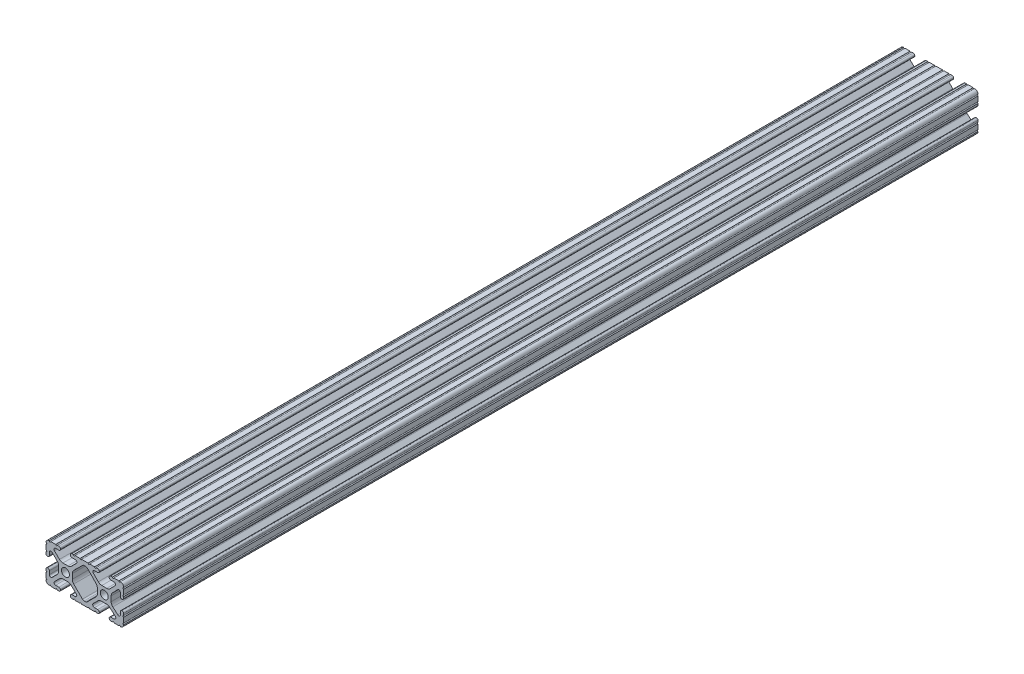
SolidWorks part; units mm, degrees
ref_plane "Front Plane" through (0, 0, 0) normal (0, 0, 1) x (1, 0, 0)
ref_plane "Top Plane" through (0, 0, 0) normal (0, 1, 0) x (1, 0, 0)
ref_plane "Right Plane" through (0, 0, 0) normal (1, 0, 0) x (0, 0, -1)
sketch "Sketch1" plane through (0, 0, 0) normal (0, 0, 1) x (1, 0, 0)
  line L0 (-7.2595, -3.8694) -> (-1.5457, -9.5728)
  line L1 (-8.1915, 1.6223) -> (-8.1915, -1.6223)
  line L2 (-1.504, 9.5765) -> (-7.252, 3.8768)
  line L3 (0.5515, 10.033) -> (-0.3952, 10.033)
  line L4 (7.2829, 3.8459) -> (1.6756, 9.5611)
  line L5 (8.1915, -1.6223) -> (8.1915, 1.6223)
  line L6 (1.5457, -9.5728) -> (7.2595, -3.8694)
  line L7 (-0.4332, -10.033) -> (0.4332, -10.033)
  line L8 (18.0171, 12.7) -> (16.9875, 12.7)
  line L9 (15.9385, 11.651) -> (15.9385, 11.5392)
  line L10 (16.9875, 10.4902) -> (19.1164, 10.4902)
  line L11 (19.8441, 8.7652) -> (16.619, 5.4551)
  line L12 (14.3449, 4.4958) -> (11.0833, 4.4958)
  line L13 (8.817, 5.4472) -> (5.5642, 8.7627)
  line L14 (6.2894, 10.4902) -> (8.4125, 10.4902)
  line L15 (9.4615, 11.5392) -> (9.4615, 11.651)
  line L16 (8.4125, 12.7) -> (7.3829, 12.7)
  line L17 (6.3669, 12.7) -> (3.1496, 12.7)
  line L18 (2.1336, 12.7) -> (-2.1336, 12.7)
  line L19 (-3.1496, 12.7) -> (-6.3669, 12.7)
  line L20 (-7.3829, 12.7) -> (-8.4125, 12.7)
  line L21 (-9.4615, 11.651) -> (-9.4615, 11.5392)
  line L22 (-8.4125, 10.4902) -> (-6.2836, 10.4902)
  line L23 (-5.5326, 8.6661) -> (-8.81, 5.4163)
  line L24 (-11.0455, 4.4958) -> (-14.3545, 4.4958)
  line L25 (-16.59, 5.4163) -> (-19.8674, 8.6661)
  line L26 (-19.1164, 10.4902) -> (-16.9875, 10.4902)
  line L27 (-15.9385, 11.5392) -> (-15.9385, 11.651)
  line L28 (-16.9875, 12.7) -> (-18.0171, 12.7)
  line L29 (-19.0331, 12.7) -> (-22.2504, 12.7)
  line L30 (-25.4, 9.5504) -> (-25.4, 6.3331)
  line L31 (-25.4, 5.3171) -> (-25.4, 4.2375)
  line L32 (-24.401, 3.2385) -> (-24.2392, 3.2385)
  line L33 (-23.1902, 4.2875) -> (-23.1902, 6.3347)
  line L34 (-21.434, 7.0665) -> (-18.148, 3.8082)
  line L35 (-17.2085, 1.5536) -> (-17.2085, -1.6952)
  line L36 (-18.1405, -3.9423) -> (-21.4316, -7.2274)
  line L37 (-23.1902, -6.498) -> (-23.1902, -4.2875)
  line L38 (-24.2392, -3.2385) -> (-24.351, -3.2385)
  line L39 (-25.4, -4.2875) -> (-25.4, -5.3171)
  line L40 (-25.4, -6.3331) -> (-25.4, -9.5504)
  line L41 (-22.2504, -12.7) -> (-19.0331, -12.7)
  line L42 (-18.0171, -12.7) -> (-16.9875, -12.7)
  line L43 (-15.9384, -11.651) -> (-15.9384, -11.5392)
  line L44 (-16.9875, -10.4902) -> (-19.1164, -10.4902)
  line L45 (-19.8341, -8.7551) -> (-16.4966, -5.4237)
  line L46 (-14.2536, -4.4958) -> (-11.1464, -4.4958)
  line L47 (-8.9034, -5.4237) -> (-5.5659, -8.7551)
  line L48 (-6.2836, -10.4902) -> (-8.4125, -10.4902)
  line L49 (-9.4616, -11.5392) -> (-9.4616, -11.651)
  line L50 (-8.4125, -12.7) -> (-7.3829, -12.7)
  line L51 (-6.3669, -12.7) -> (-3.1496, -12.7)
  line L52 (-2.1336, -12.7) -> (2.1336, -12.7)
  line L53 (3.1496, -12.7) -> (6.3669, -12.7)
  line L54 (7.3829, -12.7) -> (8.4125, -12.7)
  line L55 (9.4616, -11.651) -> (9.4616, -11.5392)
  line L56 (8.4125, -10.4902) -> (6.2894, -10.4902)
  line L57 (5.4807, -8.5353) -> (8.5979, -5.4237)
  line L58 (10.8409, -4.4958) -> (14.1026, -4.4958)
  line L59 (16.1879, -5.2766) -> (19.8682, -8.4822)
  line L60 (19.1164, -10.4902) -> (16.9875, -10.4902)
  line L61 (15.9384, -11.5392) -> (15.9384, -11.651)
  line L62 (16.9875, -12.7) -> (18.0171, -12.7)
  line L63 (19.0331, -12.7) -> (22.2504, -12.7)
  line L64 (25.4, -9.5504) -> (25.4, -6.3331)
  line L65 (25.4, -5.3171) -> (25.4, -4.2375)
  line L66 (24.401, -3.2385) -> (24.1892, -3.2385)
  line L67 (23.1902, -4.2375) -> (23.1902, -6.1559)
  line L68 (21.584, -6.8869) -> (18.2982, -4.025)
  line L69 (17.2085, -1.6308) -> (17.2085, 1.6308)
  line L70 (18.1094, 3.8465) -> (21.5263, 7.3534)
  line L71 (23.1902, 6.6769) -> (23.1902, 4.2375)
  line L72 (24.1892, 3.2385) -> (24.401, 3.2385)
  line L73 (25.4, 4.2375) -> (25.4, 5.3171)
  line L74 (25.4, 6.3332) -> (25.4, 9.5504)
  line L75 (22.2504, 12.7) -> (19.0331, 12.7)
  circle A0 centre (-12.7, 0) radius 2.6035
  circle A1 centre (12.7, 0) radius 2.6035
  arc A2 (-1.5457, -9.5728) -> (-0.4332, -10.033) centre (-0.4332, -8.4582) ccw
  arc A3 (-8.1915, -1.6223) -> (-7.2595, -3.8694) centre (-5.0165, -1.6223) ccw
  arc A4 (-7.252, 3.8768) -> (-8.1915, 1.6223) centre (-5.0165, 1.6223) ccw
  arc A5 (-0.3952, 10.033) -> (-1.504, 9.5765) centre (-0.3952, 8.4582) ccw
  arc A6 (1.6756, 9.5611) -> (0.5515, 10.033) centre (0.5515, 8.4582) ccw
  arc A7 (8.1915, 1.6223) -> (7.2829, 3.8459) centre (5.0165, 1.6223) ccw
  arc A8 (7.2595, -3.8694) -> (8.1915, -1.6223) centre (5.0165, -1.6223) ccw
  arc A9 (0.4332, -10.033) -> (1.5457, -9.5728) centre (0.4332, -8.4582) ccw
  arc A10 (18.0171, 12.7) -> (19.0331, 12.7) centre (18.5251, 12.7) ccw
  arc A11 (16.9875, 12.7) -> (15.9385, 11.651) centre (16.9875, 11.651) ccw
  arc A12 (15.9385, 11.5392) -> (16.9875, 10.4902) centre (16.9875, 11.5392) ccw
  arc A13 (19.8441, 8.7652) -> (19.1164, 10.4902) centre (19.1164, 9.4742) ccw
  arc A14 (14.3449, 4.4958) -> (16.619, 5.4551) centre (14.3449, 7.6708) ccw
  arc A15 (8.817, 5.4472) -> (11.0833, 4.4958) centre (11.0833, 7.6708) ccw
  arc A16 (6.2894, 10.4902) -> (5.5642, 8.7627) centre (6.2894, 9.4742) ccw
  arc A17 (8.4125, 10.4902) -> (9.4615, 11.5392) centre (8.4125, 11.5392) ccw
  arc A18 (9.4615, 11.651) -> (8.4125, 12.7) centre (8.4125, 11.651) ccw
  arc A19 (6.3669, 12.7) -> (7.3829, 12.7) centre (6.8749, 12.7) ccw
  arc A20 (2.1336, 12.7) -> (3.1496, 12.7) centre (2.6416, 12.7) ccw
  arc A21 (-3.1496, 12.7) -> (-2.1336, 12.7) centre (-2.6416, 12.7) ccw
  arc A22 (-7.3829, 12.7) -> (-6.3669, 12.7) centre (-6.8749, 12.7) ccw
  arc A23 (-8.4125, 12.7) -> (-9.4615, 11.651) centre (-8.4125, 11.651) ccw
  arc A24 (-9.4615, 11.5392) -> (-8.4125, 10.4902) centre (-8.4125, 11.5392) ccw
  arc A25 (-5.5326, 8.6661) -> (-6.2836, 10.4902) centre (-6.2836, 9.4235) ccw
  arc A26 (-11.0455, 4.4958) -> (-8.81, 5.4163) centre (-11.0455, 7.6708) ccw
  arc A27 (-16.59, 5.4163) -> (-14.3545, 4.4958) centre (-14.3545, 7.6708) ccw
  arc A28 (-19.1164, 10.4902) -> (-19.8674, 8.6661) centre (-19.1164, 9.4235) ccw
  arc A29 (-16.9875, 10.4902) -> (-15.9385, 11.5392) centre (-16.9875, 11.5392) ccw
  arc A30 (-15.9385, 11.651) -> (-16.9875, 12.7) centre (-16.9875, 11.651) ccw
  arc A31 (-19.0331, 12.7) -> (-18.0171, 12.7) centre (-18.5251, 12.7) ccw
  arc A32 (-23.2664, 12.6998) -> (-22.2504, 12.7) centre (-22.7584, 12.7) ccw
  arc A33 (-23.2664, 12.6998) -> (-25.3998, 10.5664) centre (-23.2918, 10.5918) ccw
  arc A34 (-25.4, 9.5504) -> (-25.3998, 10.5664) centre (-25.4, 10.0584) ccw
  arc A35 (-25.4, 5.3171) -> (-25.4, 6.3331) centre (-25.4, 5.8251) ccw
  arc A36 (-25.4, 4.2375) -> (-24.401, 3.2385) centre (-24.401, 4.2375) ccw
  arc A37 (-24.2392, 3.2385) -> (-23.1902, 4.2875) centre (-24.2392, 4.2875) ccw
  arc A38 (-21.434, 7.0665) -> (-23.1902, 6.3347) centre (-22.1596, 6.3347) ccw
  arc A39 (-17.2085, 1.5536) -> (-18.148, 3.8082) centre (-20.3835, 1.5536) ccw
  arc A40 (-18.1405, -3.9423) -> (-17.2085, -1.6952) centre (-20.3835, -1.6952) ccw
  arc A41 (-23.1902, -6.498) -> (-21.4316, -7.2274) centre (-22.1596, -6.498) ccw
  arc A42 (-23.1902, -4.2875) -> (-24.2392, -3.2385) centre (-24.2392, -4.2875) ccw
  arc A43 (-24.351, -3.2385) -> (-25.4, -4.2875) centre (-24.351, -4.2875) ccw
  arc A44 (-25.4, -6.3331) -> (-25.4, -5.3171) centre (-25.4, -5.8251) ccw
  arc A45 (-25.3998, -10.5664) -> (-25.4, -9.5504) centre (-25.4, -10.0584) ccw
  arc A46 (-25.3998, -10.5664) -> (-23.2664, -12.6998) centre (-23.2918, -10.5918) ccw
  arc A47 (-22.2504, -12.7) -> (-23.2664, -12.6998) centre (-22.7584, -12.7) ccw
  arc A48 (-18.0171, -12.7) -> (-19.0331, -12.7) centre (-18.5251, -12.7) ccw
  arc A49 (-16.9875, -12.7) -> (-15.9384, -11.651) centre (-16.9875, -11.651) ccw
  arc A50 (-15.9384, -11.5392) -> (-16.9875, -10.4902) centre (-16.9875, -11.5392) ccw
  arc A51 (-19.8341, -8.7551) -> (-19.1164, -10.4902) centre (-19.1164, -9.4742) ccw
  arc A52 (-14.2536, -4.4958) -> (-16.4966, -5.4237) centre (-14.2536, -7.6708) ccw
  arc A53 (-8.9034, -5.4237) -> (-11.1464, -4.4958) centre (-11.1464, -7.6708) ccw
  arc A54 (-6.2836, -10.4902) -> (-5.5659, -8.7551) centre (-6.2836, -9.4742) ccw
  arc A55 (-8.4125, -10.4902) -> (-9.4616, -11.5392) centre (-8.4125, -11.5392) ccw
  arc A56 (-9.4616, -11.651) -> (-8.4125, -12.7) centre (-8.4125, -11.651) ccw
  arc A57 (-6.3669, -12.7) -> (-7.3829, -12.7) centre (-6.8749, -12.7) ccw
  arc A58 (-2.1336, -12.7) -> (-3.1496, -12.7) centre (-2.6416, -12.7) ccw
  arc A59 (3.1496, -12.7) -> (2.1336, -12.7) centre (2.6416, -12.7) ccw
  arc A60 (7.3829, -12.7) -> (6.3669, -12.7) centre (6.8749, -12.7) ccw
  arc A61 (8.4125, -12.7) -> (9.4616, -11.651) centre (8.4125, -11.651) ccw
  arc A62 (9.4616, -11.5392) -> (8.4125, -10.4902) centre (8.4125, -11.5392) ccw
  arc A63 (5.4807, -8.5353) -> (6.2894, -10.4902) centre (6.2894, -9.3455) ccw
  arc A64 (10.8409, -4.4958) -> (8.5979, -5.4237) centre (10.8409, -7.6708) ccw
  arc A65 (16.1879, -5.2766) -> (14.1026, -4.4958) centre (14.1026, -7.6708) ccw
  arc A66 (19.1164, -10.4902) -> (19.8682, -8.4822) centre (19.1164, -9.3455) ccw
  arc A67 (16.9875, -10.4902) -> (15.9384, -11.5392) centre (16.9875, -11.5392) ccw
  arc A68 (15.9384, -11.651) -> (16.9875, -12.7) centre (16.9875, -11.651) ccw
  arc A69 (19.0331, -12.7) -> (18.0171, -12.7) centre (18.5251, -12.7) ccw
  arc A70 (23.2664, -12.6998) -> (22.2504, -12.7) centre (22.7584, -12.7) ccw
  arc A71 (23.2664, -12.6998) -> (25.3998, -10.5664) centre (23.2918, -10.5918) ccw
  arc A72 (25.4, -9.5504) -> (25.3998, -10.5664) centre (25.4, -10.0584) ccw
  arc A73 (25.4, -5.3171) -> (25.4, -6.3331) centre (25.4, -5.8251) ccw
  arc A74 (25.4, -4.2375) -> (24.401, -3.2385) centre (24.401, -4.2375) ccw
  arc A75 (24.1892, -3.2385) -> (23.1902, -4.2375) centre (24.1892, -4.2375) ccw
  arc A76 (21.584, -6.8869) -> (23.1902, -6.1559) centre (22.2207, -6.1559) ccw
  arc A77 (17.2085, -1.6308) -> (18.2982, -4.025) centre (20.3835, -1.6308) ccw
  arc A78 (18.1094, 3.8465) -> (17.2085, 1.6308) centre (20.3835, 1.6308) ccw
  arc A79 (23.1902, 6.6769) -> (21.5263, 7.3534) centre (22.2207, 6.6769) ccw
  arc A80 (23.1902, 4.2375) -> (24.1892, 3.2385) centre (24.1892, 4.2375) ccw
  arc A81 (24.401, 3.2385) -> (25.4, 4.2375) centre (24.401, 4.2375) ccw
  arc A82 (25.4, 6.3332) -> (25.4, 5.3171) centre (25.4, 5.8251) ccw
  arc A83 (25.3998, 10.5664) -> (25.4, 9.5504) centre (25.4, 10.0584) ccw
  arc A84 (25.3998, 10.5664) -> (23.2664, 12.6998) centre (23.2918, 10.5918) ccw
  arc A85 (22.2504, 12.7) -> (23.2664, 12.6998) centre (22.7584, 12.7) ccw
  point P248 (0, 10.033)
extrude "Boss-Extrude1" add sketch "Sketch1" along normal mid plane 558.8
sketch "Sketch2" plane through (0, 4.4958, 0) normal (0, 1, 0) x (1, 0, 0)
  line L0 (0, 0) -> (45.9739, 0) construction
  line L1 (0, 0) -> (0, 22.9841) construction
  line L2 (-11.0455, -279.4) -> (-14.3545, -279.4) construction
  circle A0 centre (-12.7, -254) radius 3.175
  circle A1 centre (-12.7, 254) radius 3.175
  circle A2 centre (12.7, 254) radius 3.175
  circle A3 centre (12.7, -254) radius 3.175
  dimension "D1" = 6.35
  dimension "D2" = 25.4
extrude "Cut-Extrude1" cut sketch "Sketch2" against normal through all both and the other way through all
